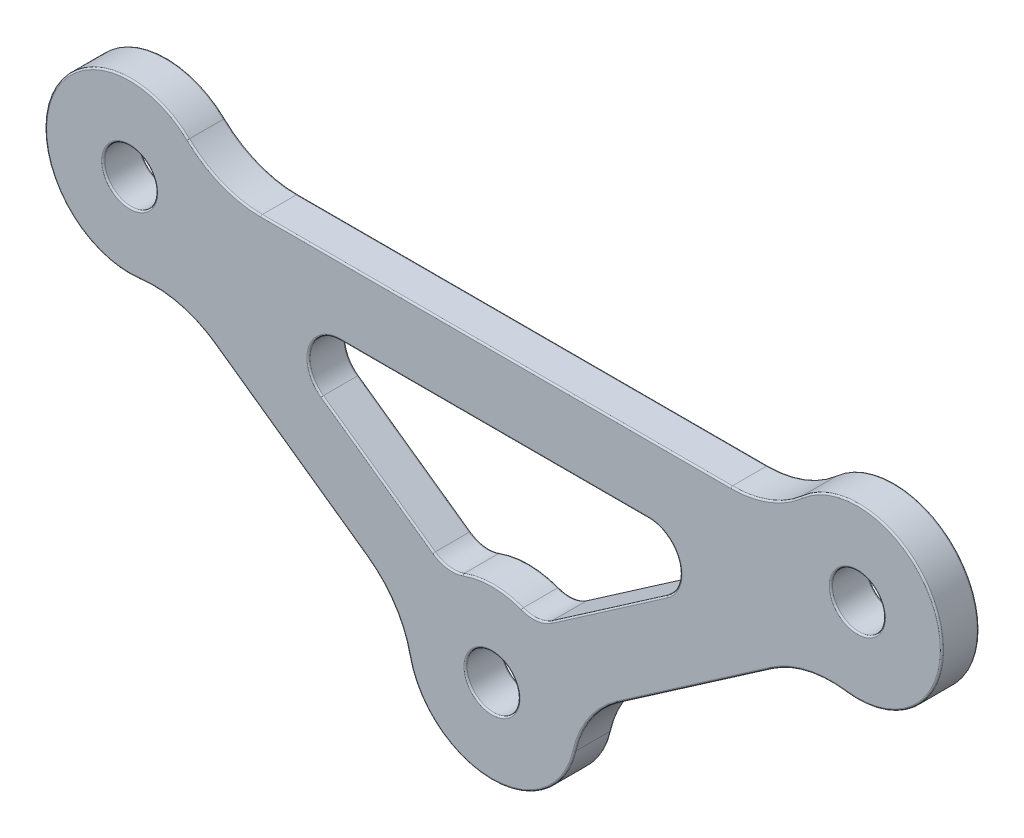
SolidWorks part; units mm, degrees
ref_plane "Front Plane" through (0, 0, 0) normal (0, 0, 1) x (1, 0, 0)
ref_plane "Top Plane" through (0, 0, 0) normal (0, 1, 0) x (1, 0, 0)
ref_plane "Right Plane" through (0, 0, 0) normal (1, 0, 0) x (0, 0, -1)
sketch "Sketch1" plane through (0, 0, 0) normal (0, 0, 1) x (1, 0, 0)
  line L0 (-52.5327, 202.0095) -> (-17.9832, 225.8913) construction
  line L1 (-17.9832, 225.8913) -> (-86.7908, 226.3073) construction
  line L2 (-86.7908, 226.3073) -> (-52.5327, 202.0095) construction
  line L3 (-52.5327, 202.0095) -> (-17.9832, 225.8913) construction
  line L4 (-17.9832, 225.8913) -> (-86.7908, 226.3073) construction
  line L5 (-86.7908, 226.3073) -> (-52.5327, 202.0095) construction
  circle A0 centre (-86.7908, 226.3073) radius 8
  circle A1 centre (-52.5327, 202.0095) radius 8
  circle A2 centre (-17.9832, 225.8913) radius 8
  circle A3 centre (-86.7908, 226.3073) radius 2.5
  circle A4 centre (-52.5327, 202.0095) radius 2.5
  circle A5 centre (-17.9832, 225.8913) radius 2.5
  dimension "D1" = 16
  dimension "D2" = 5
  dimension "D3" = 5
extrude "Boss-Extrude1" add sketch "Sketch1" against normal blind 3.5
sketch "Sketch2" plane through (0, 0, 0) normal (0, 0, 1) x (1, 0, 0)
  line L0 (-79.887, 226.0993) -> (-24.887, 226.0993)
  line L1 (-47.597, 205.4212) -> (-22.9189, 222.4796)
  line L2 (-57.4267, 205.4807) -> (-81.8967, 222.8362)
  line L3 (-17.9832, 225.8913) -> (-86.7908, 226.3073) construction
  line L4 (-86.7908, 226.3073) -> (-52.5327, 202.0095) construction
  line L5 (-52.5327, 202.0095) -> (-17.9832, 225.8913) construction
  point P6 (-52.387, 226.0993)
  point P9 (-52.387, 226.0993)
  point P17 (-69.6617, 214.1584)
  point P18 (-69.6617, 214.1584)
  point P20 (-35.258, 213.9504)
  point P21 (-35.258, 213.9504)
  dimension "D1" = 55
  dimension "D2" = 30
extrude "Extrude-Thin1" add sketch "Sketch2" against normal blind 3.5 thin thin type mid plane wall 6.5
fillet "Fillet1" radius 3 4 edges at (-28.0997, 222.8493, -1.75) (-76.2974, 222.8493, -1.75) (-48.3673, 208.8396, -1.75) (-56.6151, 208.8895, -1.75)
fillet "Fillet2" radius 10 6 edges at (-44.6714, 203.4927, -1.75) (-22.1486, 219.0612, -1.75) (-60.3755, 203.5876, -1.75) (-82.7083, 219.4274, -1.75) (-25.1973, 229.3493, -1.75) (-79.3917, 229.3493, -1.75)
fillet "Fillet3" radius 0.15 46 edges at (-50.0327, 202.0095, -3.5) (-15.4832, 225.8913, -3.5) (-84.2908, 226.3073, -3.5) (-43.2621, 203.6364, -3.5) (-33.41, 211.2769, 0) (-33.41, 211.2769, -3.5) (-22.781, 217.7937, -3.5) (-10.326, 228.2079, -3.5) (-26.3846, 230.0014, -3.5) (-52.1607, 229.3493, 0) (-52.1607, 229.3493, -3.5) (-78.0959, 230.0634, -3.5) (-94.3924, 228.8004, -3.5) (-82.0913, 218.1523, -3.5) (-71.5419, 211.5075, -3.5) (-71.5419, 211.5075, 0) (-61.7829, 203.7484, -3.5) (-52.581, 194.0097, -3.5) (-34.8519, 220.7428, -3.5) (-41.4722, 213.6058, 0) (-41.4722, 213.6058, -3.5) (-48.2765, 209.32, -3.5) (-52.4843, 210.0094, -3.5) (-56.7001, 209.3709, -3.5) (-63.3267, 213.6497, -3.5) (-63.3267, 213.6497, 0) (-69.7404, 220.7601, -3.5) (-52.2989, 222.8493, -3.5) (-52.2989, 222.8493, 0) (-50.0327, 202.0095, 0) (-15.4832, 225.8913, 0) (-84.2908, 226.3073, 0) (-26.3846, 230.0014, 0) (-10.326, 228.2079, 0) (-22.781, 217.7937, 0) (-43.2621, 203.6364, 0) (-52.581, 194.0097, 0) (-61.7829, 203.7484, 0) (-82.0913, 218.1523, 0) (-94.3924, 228.8004, 0) (-78.0959, 230.0634, 0) (-48.2765, 209.32, 0) (-34.8519, 220.7428, 0) (-69.7404, 220.7601, 0) (-56.7001, 209.3709, 0) (-52.4843, 210.0094, 0)
